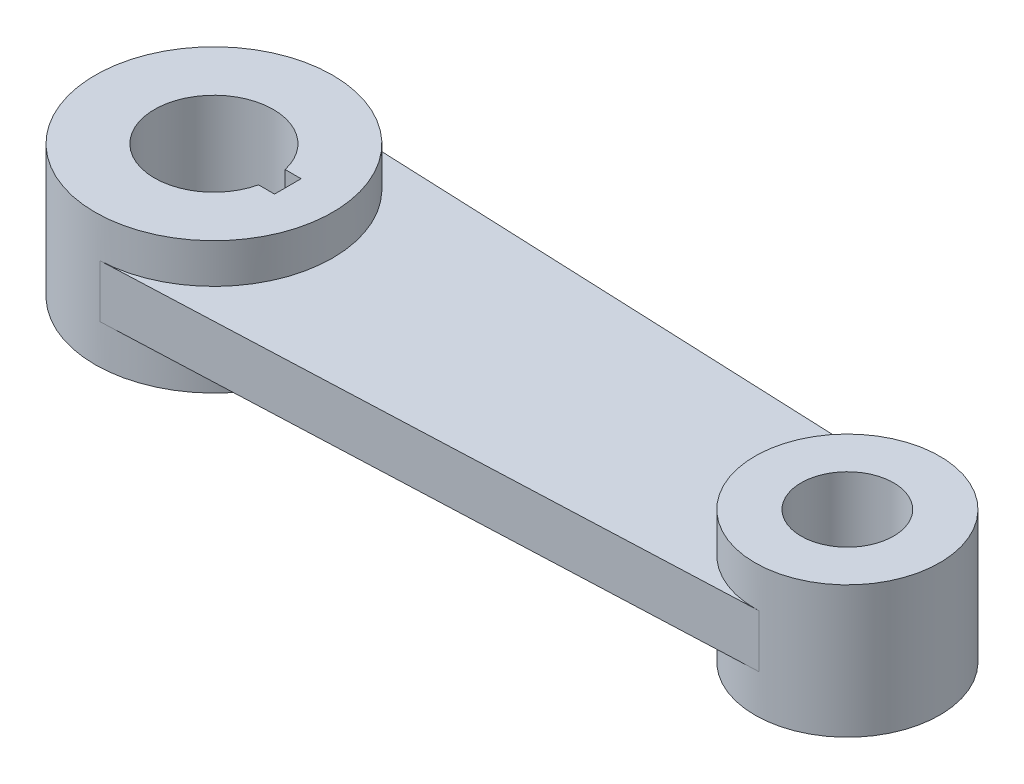
SolidWorks part; units mm, degrees
ref_plane "Front Plane" through (0, 0, 0) normal (0, 0, 1) x (1, 0, 0)
ref_plane "Top Plane" through (0, 0, 0) normal (0, 1, 0) x (1, 0, 0)
ref_plane "Right Plane" through (0, 0, 0) normal (1, 0, 0) x (0, 0, -1)
sketch "Sketch1" plane through (0, 0, 0) normal (0, 1, 0) x (1, 0, 0)
  line L0 (35, 6.3) -> (35, -6.3)
  line L1 (35, 6.3) -> (27.436, 6.3)
  line L2 (35, -6.3) -> (27.436, -6.3)
  arc A0 (27.436, 6.3) -> (27.436, -6.3) centre (0, 0) ccw
  circle A1 centre (0, 0) radius 56.25
  circle A2 centre (300, 0) radius 21.9
  circle A3 centre (300, 0) radius 43.75
  dimension "D1" = 112.5
  dimension "D2" = 56.3
  dimension "D3" = 87.5
  dimension "D4" = 43.8
  dimension "D5" = 300
  dimension "D6" = 12.6
  dimension "D7" = 6.3
  dimension "D8" = 35
extrude "Boss-Extrude1" add sketch "Sketch1" along normal mid plane 62.5
sketch "Sketch2" plane through (0, 0, 0) normal (0, 1, 0) x (1, 0, 0)
  line L0 (2.3437, 56.2012) -> (301.8229, 43.712)
  line L1 (2.3437, -56.2012) -> (301.8229, -43.712)
  circle A0 centre (0, 0) radius 56.25 construction
  circle A1 centre (300, 0) radius 43.75 construction
  arc A2 (2.3437, -56.2012) -> (2.3437, 56.2012) centre (0, 0) ccw
  arc A3 (301.8229, 43.712) -> (301.8229, -43.712) centre (300, 0) ccw
extrude "Boss-Extrude2" add sketch "Sketch2" against normal blind 25 from offset 12.5
